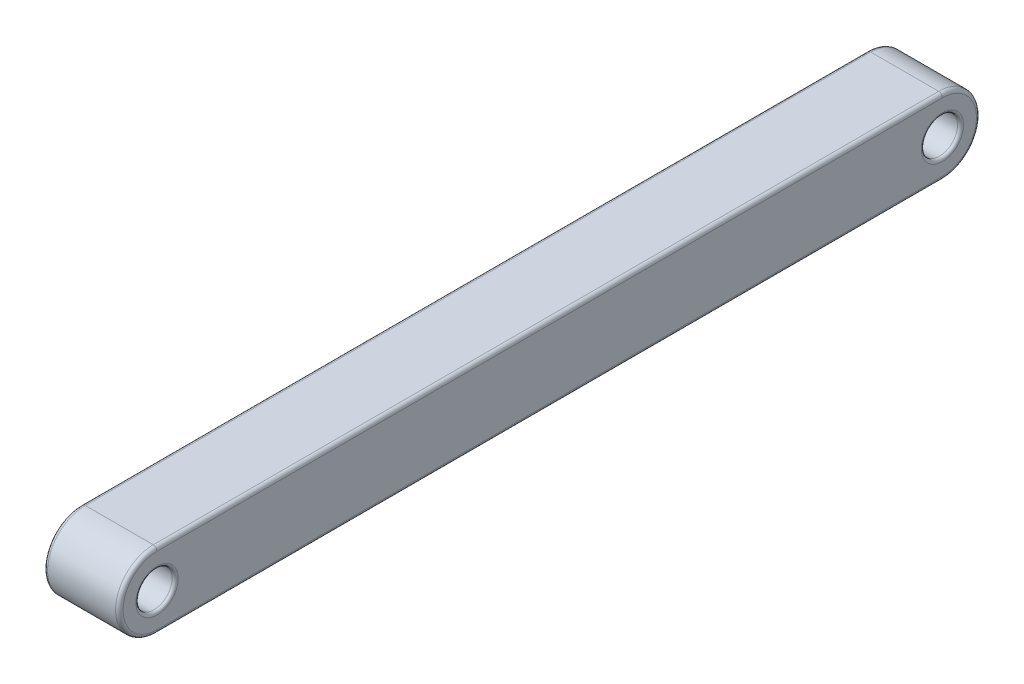
SolidWorks part; units mm, degrees
ref_plane "Front Plane" through (0, 0, 0) normal (0, 0, 1) x (1, 0, 0)
ref_plane "Top Plane" through (0, 0, 0) normal (0, 1, 0) x (1, 0, 0)
ref_plane "Right Plane" through (0, 0, 0) normal (1, 0, 0) x (0, 0, -1)
sketch "Sketch1" plane through (0, 0, 0) normal (1, 0, 0) x (0, 0, -1)
  line L1 (0, 0) -> (24, 0)
  line L2 (0, 0) -> (0, -2.5) construction
  line L3 (0, -2.5) -> (24, -2.5)
  line L4 (24, 0) -> (24, -2.5) construction
  line L5 (0, 0) -> (-1, 0)
  line L6 (0, 0) -> (0, -2.5) construction
  line L7 (0, -2.5) -> (-1, -2.5)
  line L8 (-1, 0) -> (-1, -2.5) construction
  line L9 (24, 0) -> (25, 0)
  line L10 (24, 0) -> (24, -2.5) construction
  line L11 (24, -2.5) -> (25, -2.5)
  line L12 (25, 0) -> (25, -2.5) construction
  line L16 (0, -1.25) -> (-1, -1.25) construction
  line L17 (24, -1.25) -> (25, -1.25) construction
  circle A0 centre (-1, -1.25) radius 0.6
  arc A1 (-1, -2.5) -> (-1, 0) centre (-1, -1.25) cw
  circle A2 centre (25, -1.25) radius 0.6
  arc A3 (25, 0) -> (25, -2.5) centre (25, -1.25) cw
  dimension "D1" = 1.2
  dimension "D4" = 1.2
  dimension "D2" = 2.5
  dimension "D3" = 2.5
  dimension "D5" = 26
  dimension "D6" = 2.5
  dimension "D7" = 1
  dimension "D8" = 1
extrude "Boss-Extrude1" add sketch "Sketch1" along normal blind 2.5 contours A3 L9 L1 L5 A1 L7 L3 L11 A2 A0
fillet "Fillet1" radius 0.125 8 edges at (2.5, -1.25, -26.25) (2.5, 0, -12) (2.5, -1.25, 2.25) (0, -1.25, -26.25) (0, 0, -12) (0, -1.25, 2.25) (2.5, -2.5, -12) (0, -2.5, -12)
fillet "Fillet2" radius 0.1 4 edges at (0, -1.25, -25.6) (2.5, -1.25, -25.6) (0, -1.25, 0.4) (2.5, -1.25, 0.4)
